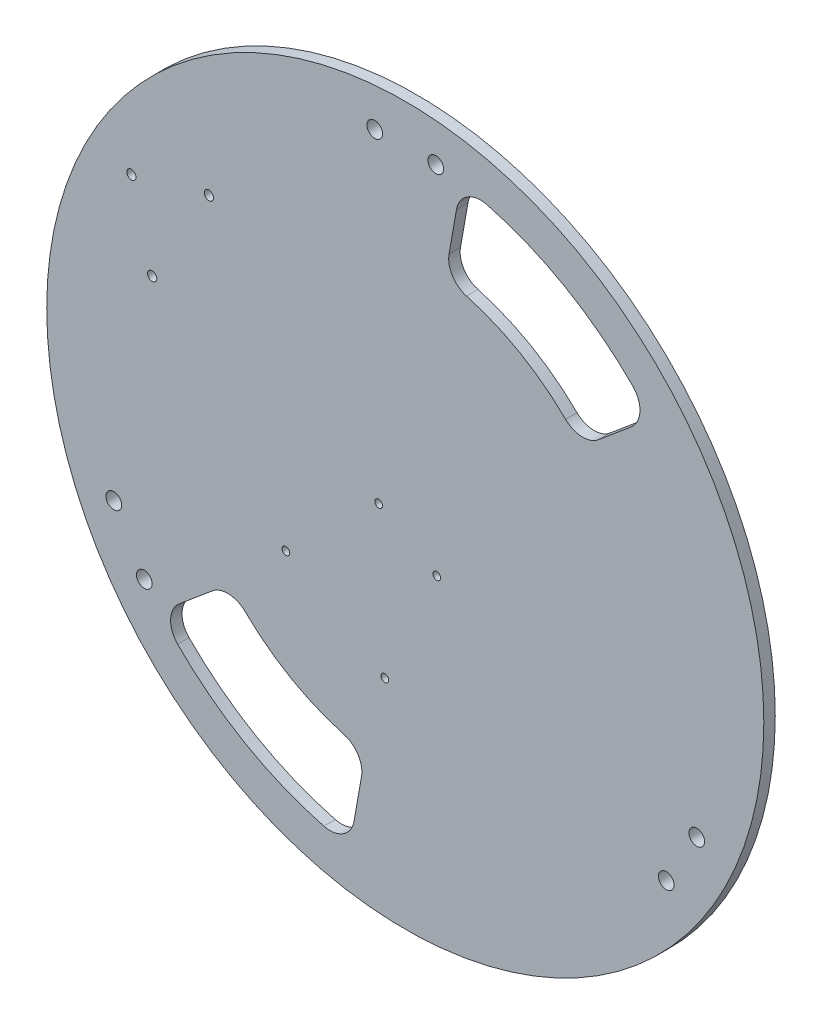
SolidWorks part; units mm, degrees
material "Acrylic (Medium-high impact)"
ref_plane "Front Plane" through (0, 0, 0) normal (0, 0, 1) x (1, 0, 0)
ref_plane "Top Plane" through (0, 0, 0) normal (0, 1, 0) x (1, 0, 0)
ref_plane "Right Plane" through (0, 0, 0) normal (1, 0, 0) x (0, 0, -1)
sketch "Sketch1" plane through (0, 0, 0) normal (0, 0, 1) x (1, 0, 0)
  arc A0 (-68.7189, -132.4606) -> (130.0374, -73.2009) centre (0, 0) ccw
  arc A6 (128.4125, -76.0153) -> (-80.3548, -125.7426) centre (0, 0) ccw
  arc A7 (-80.3548, -125.7426) -> (-68.7189, -132.4606) centre (0, 0) ccw
  circle A11 centre (0, 0) radius 148.3041 construction
  point P17 (9.525, 148.9207)
  point P18 (0, 0)
  point P20 (9.525, 88.3883)
  point P31 (-125.4647, -61.4386)
  point P122 (0, 0)
  point P151 (0, 0)
  dimension "D2" = 298.45
extrude "Boss-Extrude1" add sketch "Sketch1" along normal blind 4.762
sketch "Sketch5" plane through (0, 0, 4.762) normal (0, 0, 1) x (1, 0, 0)
  circle A0 centre (-81.7197, 74.4573) radius 1.9266 construction
  circle A1 centre (-113.988, 65.811) radius 1.9266 construction
  circle A2 centre (-105.3417, 33.5427) radius 1.9266 construction
  circle A3 centre (-81.7197, 74.4573) radius 1.9266
  circle A4 centre (-113.988, 65.811) radius 1.9266
  circle A5 centre (-105.3417, 33.5427) radius 1.9266
  dimension "D1" = 3.8533
extrude "motor_mounting_holes" cut sketch "Sketch5" against normal through all
sketch "Sketch6" plane through (0, 0, 4.762) normal (0, 0, 1) x (1, 0, 0)
  line L2 (130.6322, -75.4205) -> (0, 0) construction
  circle A0 centre (0, 0) radius 16.0299
sketch "Sketch7" plane through (0, 0, 0) normal (0, 0, -1) x (-1, 0, 0)
  line L16 (11.9028, -69.3843) -> (54.0492, -45.0511)
  line L17 (7.9932, -68.7086) -> (11.9028, -69.3843)
  line L18 (-18.626, -22.6028) -> (7.9932, -68.7086)
  line L19 (-20.9628, -18.5553) -> (-18.7276, -22.4268)
  line L20 (-10.4922, -12.5101) -> (-20.9628, -18.5553)
  line L21 (-13.1479, -7.7072) -> (-10.455, -12.3714)
  line L22 (15.5015, 2.6146) -> (13.0626, 6.8388)
  line L23 (26.9907, 9.1307) -> (15.6403, 2.5775)
  line L24 (29.4799, 4.8192) -> (26.9907, 9.1307)
  line L25 (56.4547, -41.9025) -> (29.5815, 4.6433)
  line L26 (55.8969, -43.9843) -> (56.4547, -41.9025)
  line L27 (54.2252, -44.9495) -> (55.8969, -43.9843)
  line L28 (11.9028, -69.3843) -> (54.0492, -45.0511) construction
  line L29 (7.9932, -68.7086) -> (11.9028, -69.3843)
  line L30 (-18.626, -22.6028) -> (7.9932, -68.7086) construction
  line L31 (-20.9628, -18.5553) -> (-18.7276, -22.4268) construction
  line L32 (-10.4922, -12.5101) -> (-20.9628, -18.5553) construction
  line L33 (-13.1479, -7.7072) -> (-10.455, -12.3714) construction
  line L34 (15.5015, 2.6146) -> (13.0626, 6.8388) construction
  line L35 (26.9907, 9.1307) -> (15.6403, 2.5775) construction
  line L36 (29.4799, 4.8192) -> (26.9907, 9.1307) construction
  line L37 (56.4547, -41.9025) -> (29.5815, 4.6433) construction
  line L38 (55.8969, -43.9843) -> (56.4547, -41.9025) construction
  line L39 (54.2252, -44.9495) -> (55.8969, -43.9843) construction
  circle A1 centre (0, 0) radius 149.225
  circle A2 centre (0, 0) radius 149.225
  circle A3 centre (11.0825, -1.3074) radius 1.5875
  circle A4 centre (11.0825, -1.3074) radius 1.5875
  circle A5 centre (-13.1143, -15.2774) radius 1.5875
  circle A6 centre (-13.1143, -15.2774) radius 1.5875
  circle A7 centre (49.6807, -37.6815) radius 1.5875
  circle A8 centre (49.6807, -37.6815) radius 1.5875
  circle A9 centre (8.5213, -62.9114) radius 1.5875
  arc A10 (-18.626, -22.6028) -> (-18.7276, -22.4268) centre (-18.6768, -22.5148) ccw
  arc A11 (-10.4922, -12.5101) -> (-10.455, -12.3714) centre (-10.4042, -12.4593) ccw
  arc A12 (-13.1479, -7.7072) -> (-13.2476, -7.5302) centre (-13.1986, -7.6192) ccw
  arc A13 (12.9623, 7.0155) -> (-13.2476, -7.5302) centre (-0.093, -0.347) ccw
  arc A14 (12.9623, 7.0155) -> (13.0626, 6.8388) centre (13.0119, 6.9268) ccw
  arc A15 (15.5015, 2.6146) -> (15.6403, 2.5775) centre (15.5523, 2.5267) ccw
  arc A16 (29.4799, 4.8192) -> (29.5815, 4.6433) centre (29.5307, 4.7312) ccw
  arc A17 (54.2252, -44.9495) -> (54.0492, -45.0511) centre (54.1372, -45.0003) ccw
  arc A18 (-18.626, -22.6028) -> (-18.7276, -22.4268) centre (-18.6768, -22.5148) ccw construction
  arc A19 (-10.4922, -12.5101) -> (-10.455, -12.3714) centre (-10.4042, -12.4593) ccw construction
  arc A20 (-13.1479, -7.7072) -> (-13.2476, -7.5302) centre (-13.1986, -7.6192) ccw construction
  arc A21 (12.9623, 7.0155) -> (-13.2476, -7.5302) centre (-0.093, -0.347) ccw construction
  arc A22 (12.9623, 7.0155) -> (13.0626, 6.8388) centre (13.0119, 6.9268) ccw construction
  arc A23 (15.5015, 2.6146) -> (15.6403, 2.5775) centre (15.5523, 2.5267) ccw construction
  arc A24 (29.4799, 4.8192) -> (29.5815, 4.6433) centre (29.5307, 4.7312) ccw construction
  arc A25 (54.2252, -44.9495) -> (54.0492, -45.0511) centre (54.1372, -45.0003) ccw construction
  circle A26 centre (8.5213, -62.9114) radius 1.5875
  dimension "D1" = 0
  dimension "D2" = 0
  dimension "D3" = 0
  dimension "D4" = 0
  dimension "D5" = 0
  dimension "D6" = 0
extrude "arduino mounting holes" cut sketch "Sketch7" against normal through all contours A6 | A26 | A4 | A8
sketch "Sketch9" plane through (0, 0, 4.762) normal (0, 0, 1) x (1, 0, 0)
  line L0 (0, 0) -> (-93.5307, 54) construction
  line L1 (0, 0) -> (78.5473, -45.3493) construction
  line L2 (0, 0) -> (-76.1177, -43.9466) construction
  line L3 (0, 0) -> (0, 104.5482) construction
  circle A0 centre (0, 0) radius 133.35 construction
  circle A1 centre (0, 0) radius 149.225 construction
  circle A2 centre (121.3096, -55.3734) radius 3.2639
  circle A3 centre (108.6096, -77.3705) radius 3.2639
  circle A4 centre (-108.6096, -77.3705) radius 3.2639
  circle A5 centre (-121.3096, -55.3734) radius 3.2639
  circle A6 centre (-12.7, 132.7439) radius 3.2639
  circle A7 centre (12.7, 132.7439) radius 3.2639
  point P24 (0, 0)
  point P25 (17.2625, 56.34)
  dimension "D4" = 15.875
  dimension "D5" = 6.5278
  dimension "D8" = 266.7
  dimension "D1" = 180
  dimension "D2" = 120
  dimension "D3" = 120
  dimension "D6" = 12.7
  dimension "D7" = 3
extrude "1/4-20 feet holes" cut sketch "Sketch9" against normal through all
sketch "Sketch8" plane through (0, 0, 4.762) normal (0, 0, 1) x (1, 0, 0)
  line L0 (0, 0) -> (130.6322, -75.4205) construction
  line L1 (0, 0) -> (66.675, 115.4845) construction
  line L2 (21.3188, 120.9052) -> (18.219, 103.3253)
  line L3 (94.0475, 78.9152) -> (80.3728, 67.4408)
  line L4 (-94.0475, -78.9152) -> (-80.3728, -67.4408)
  line L5 (-21.3188, -120.9052) -> (-18.219, -103.3253)
  arc A0 (94.7347, 93.8486) -> (33.908, 128.9669) centre (0, 0) ccw
  circle A1 centre (0, 0) radius 149.225 construction
  arc A2 (66.7248, 67.9733) -> (25.5042, 91.772) centre (0, 0) ccw
  arc A3 (94.0475, 78.9152) -> (94.7347, 93.8486) centre (87.5168, 86.6982) ccw
  arc A4 (80.3728, 67.4408) -> (66.7248, 67.9733) centre (73.8421, 75.2238) cw
  arc A5 (18.219, 103.3253) -> (25.5042, 91.772) centre (28.2247, 101.561) ccw
  arc A6 (21.3188, 120.9052) -> (33.908, 128.9669) centre (31.3245, 119.1409) cw
  arc A7 (-80.3728, -67.4408) -> (-66.7248, -67.9733) centre (-73.8421, -75.2238) cw
  arc A8 (-94.0475, -78.9152) -> (-94.7347, -93.8486) centre (-87.5168, -86.6982) ccw
  arc A9 (-33.908, -128.9669) -> (-94.7347, -93.8486) centre (0, 0) cw
  arc A10 (-21.3188, -120.9052) -> (-33.908, -128.9669) centre (-31.3245, -119.1409) cw
  arc A11 (-18.219, -103.3253) -> (-25.5042, -91.772) centre (-28.2247, -101.561) ccw
  arc A12 (-25.5042, -91.772) -> (-66.7248, -67.9733) centre (0, 0) cw
  point P14 (102.152, 85.7157)
  point P17 (72.9657, 61.2255)
  point P20 (16.54, 93.8029)
  point P23 (23.156, 131.3241)
  dimension "D1" = 15.875
  dimension "D2" = 38.1
  dimension "D3" = 90
  dimension "D5" = 10.16
  dimension "D4" = 20
extrude "handles" cut sketch "Sketch8" against normal through all
